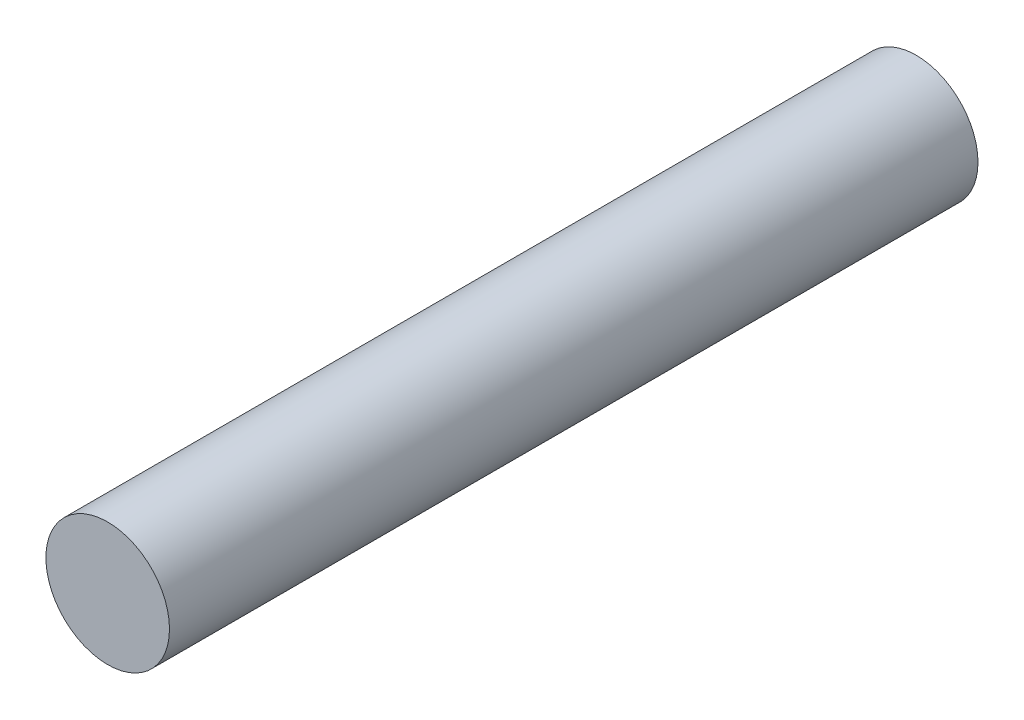
SolidWorks part; units mm, degrees
material "Plain Carbon Steel"
ref_plane "Front Plane" through (0, 0, 0) normal (0, 0, 1) x (1, 0, 0)
ref_plane "Top Plane" through (0, 0, 0) normal (0, 1, 0) x (1, 0, 0)
ref_plane "Right Plane" through (0, 0, 0) normal (1, 0, 0) x (0, 0, -1)
sketch "Sketch1" plane through (0, 0, 0) normal (0, 0, 1) x (1, 0, 0)
  circle A0 centre (0, 0) radius 6
  dimension "D1" = 12
extrude "Boss-Extrude1" add sketch "Sketch1" along normal blind 78.5
sketch "Sketch2" plane through (0, 0, 0) normal (0, 0, -1) x (-1, 0, 0)
  circle A0 centre (0, 0) radius 4.5
  dimension "D1" = 9
extrude "Cut-Extrude1" cut sketch "Sketch2" against normal blind 2.4
sketch3d "3DSketch2"
  line L0 (-1.7121, 3.615, 0.0262) -> (-3.2097, 5.0693, 78.5) construction
  line L1 (-3.9706, -2.1176, 2.4) -> (-2.1912, -1.1971, -13.4741)
  circle A1 centre (0, 0, 0) radius 4
  circle A3 centre (0, 0, 0) radius 2.5
  circle A4 centre (0, 0, 78.5) radius 6 construction
  circle A5 centre (0, 0, 2.4) radius 4.5 construction
  point P5 (0.0112, -0.0237, 3.9999)
  point P8 (0.1105, 0.0604, 2.4968)
  point P10 (0, 0, 84.5)
  point P15 (0, 0, -2.1)
  dimension "D1" = 8
  dimension "D2" = 5
  dimension "D3" = 78.5015
  dimension "D4" = 16
